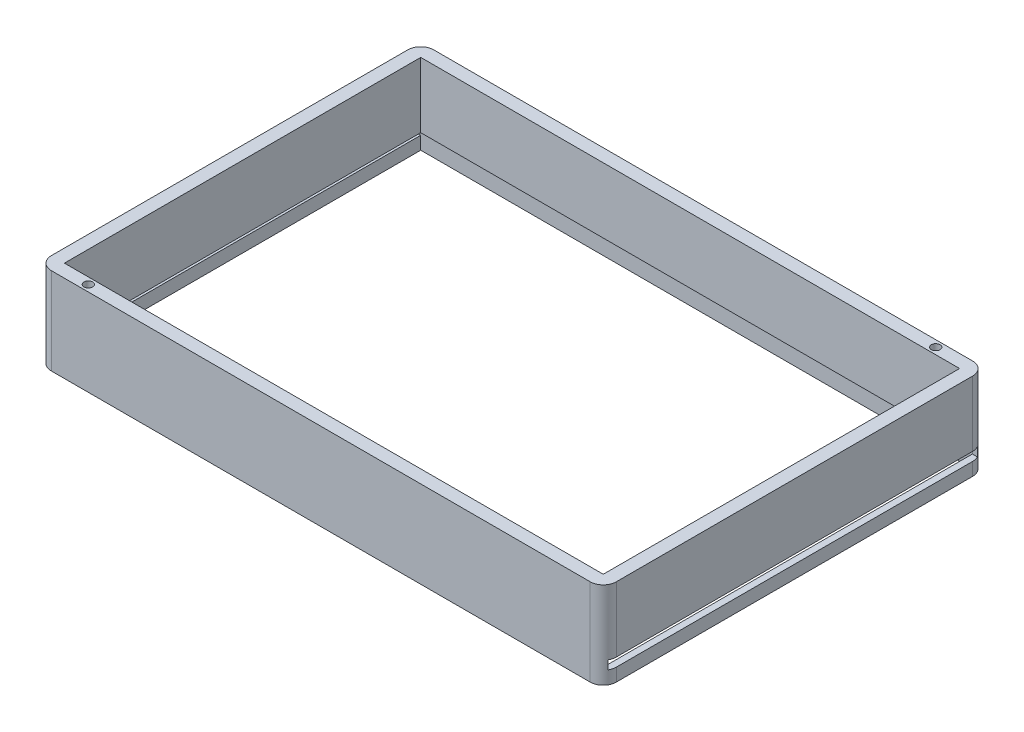
SolidWorks part; units mm, degrees
ref_plane "Спереди" through (0, 0, 0) normal (0, 0, 1) x (1, 0, 0)
ref_plane "Сверху" through (0, 0, 0) normal (0, 1, 0) x (1, 0, 0)
ref_plane "Справа" through (0, 0, 0) normal (1, 0, 0) x (0, 0, -1)
sketch "Эскиз1" plane through (0, 0, 0) normal (0, 1, 0) x (1, 0, 0)
  line L1 (3, 0) -> (127, 0)
  line L2 (0, 3) -> (0, 85)
  line L3 (3, 88) -> (127, 88)
  line L4 (130, 3) -> (130, 85)
  line L5 (3, 3) -> (127, 3)
  line L6 (3, 3) -> (3, 85)
  line L7 (3, 85) -> (127, 85)
  line L8 (127, 3) -> (127, 85)
  arc A0 (3, 0) -> (0, 3) centre (3, 3) cw
  arc A1 (0, 85) -> (3, 88) centre (3, 85) cw
  arc A2 (127, 88) -> (130, 85) centre (127, 85) cw
  arc A3 (127, 0) -> (130, 3) centre (127, 3) ccw
  circle A4 centre (120, 86.5) radius 1
  circle A5 centre (10, 1.5) radius 1
  point P7 (0, 0)
  dimension "D1" = 3
  dimension "D2" = 3
  dimension "D3" = 3
  dimension "D4" = 3
extrude "Бобышка-Вытянуть2" add sketch "Эскиз1" along normal blind 20
sketch "Эскиз2" plane through (0, 0, 0) normal (0, -1, 0) x (-1, 0, 0)
  line L1 (-1.5, 1.5) -> (-128.5, 1.5)
  line L2 (-1.5, 1.5) -> (-1.5, 86.5)
  line L3 (-1.5, 86.5) -> (-128.5, 86.5)
  line L4 (-128.5, 1.5) -> (-128.5, 86.5)
extrude "Вырез-Вытянуть1" cut sketch "Эскиз2" against normal blind 5
sketch "Эскиз3" plane through (0, 0, 0) normal (-1, 0, 0) x (0, 0, 1)
  line L1 (-1.4922, 2.9877) -> (-86.4412, 2.9877)
  line L2 (-1.4922, 2.9877) -> (-1.4922, 4.9877)
  line L3 (-1.4922, 4.9877) -> (-86.4412, 4.9877)
  line L4 (-86.4412, 2.9877) -> (-86.4412, 4.9877)
extrude "Вырез-Вытянуть3" cut sketch "Эскиз3" against normal blind 164 contours L2 L1 L4 L3
